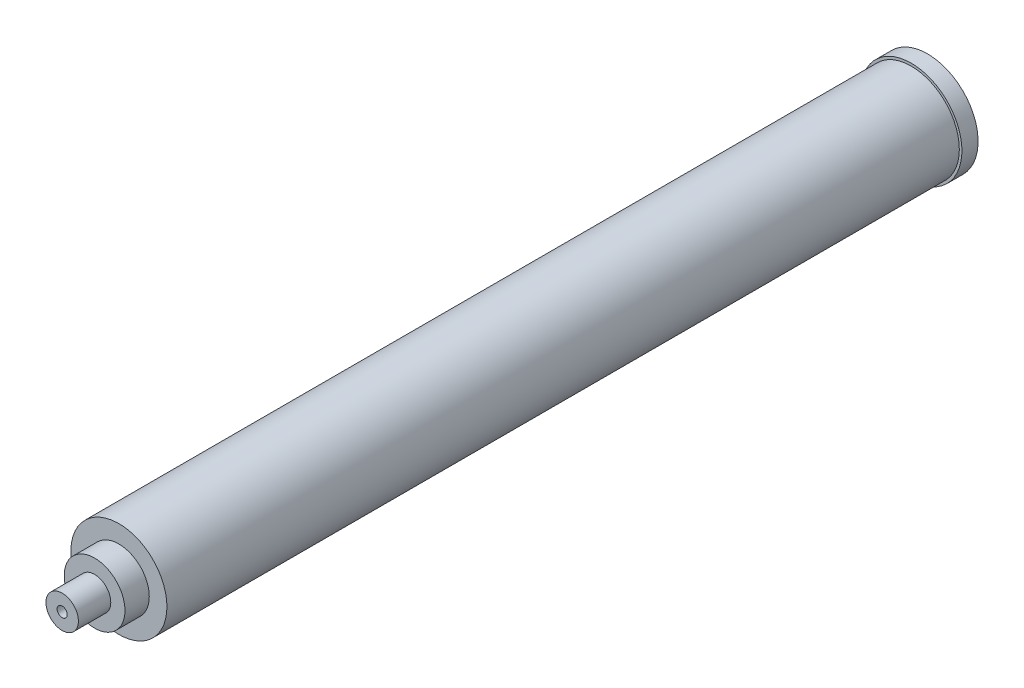
SolidWorks part; units mm, degrees
ref_plane "Front Plane" through (0, 0, 0) normal (0, 0, 1) x (1, 0, 0)
ref_plane "Top Plane" through (0, 0, 0) normal (0, 1, 0) x (1, 0, 0)
ref_plane "Right Plane" through (0, 0, 0) normal (1, 0, 0) x (0, 0, -1)
sketch "Sketch1" plane through (0, 0, 0) normal (0, 0, 1) x (1, 0, 0)
  circle A0 centre (0, 0) radius 37.6555
  dimension "D1" = 75.311
extrude "Boss-Extrude1" add sketch "Sketch1" along normal blind 621.03
sketch "Sketch2" plane through (0, 0, 0) normal (0, 0, -1) x (-1, 0, 0)
  circle A0 centre (0, 0) radius 39.6621
  dimension "D1" = 79.3242
extrude "Boss-Extrude2" add sketch "Sketch2" along normal blind 12.7
sketch "Sketch4" plane through (0, 0, 621.03) normal (0, 0, 1) x (1, 0, 0)
  circle A0 centre (0, 0) radius 23.8125
  dimension "D1" = 47.625
extrude "Boss-Extrude4" add sketch "Sketch4" along normal blind 19.05
sketch "Sketch5" plane through (0, 0, 640.08) normal (0, 0, 1) x (1, 0, 0)
  circle A0 centre (0, 0) radius 12.7
  dimension "D1" = 25.4
extrude "Boss-Extrude5" add sketch "Sketch5" along normal blind 25.4
hole_wizard "3/8-16 Tapped Hole1" positions "Sketch6" profile "Sketch7" tap size "3/8-16" standard "ANSI Inch"
sketch "Sketch6" plane through (0, 0, 665.48) normal (0, 0, 1) x (1, 0, 0)
  point P0 (0, 0)
cosmetic thread "Hole Thread1" parameters "D2"=9.525
sketch "Sketch7" plane through (0, 0, 665.48) normal (1, 0, 0) x (0, -1, 0)
  line L0 (0, 0) -> (0, 27.7847)
  line L1 (0, 27.7847) -> (3.9687, 25.4)
  line L2 (3.9687, 25.4) -> (3.9687, 0)
  line L5 (3.9687, 0) -> (0, 0)
  line L10 (0, 27.7847) -> (-3.9687, 25.4) construction
  line L11 (0, -6.35) -> (0, 107.95) construction
  dimension "Tap Drill Dia." = 7.9375
  dimension "Tap Drill Depth" = 25.4
  dimension "Drill Angle" = 118
